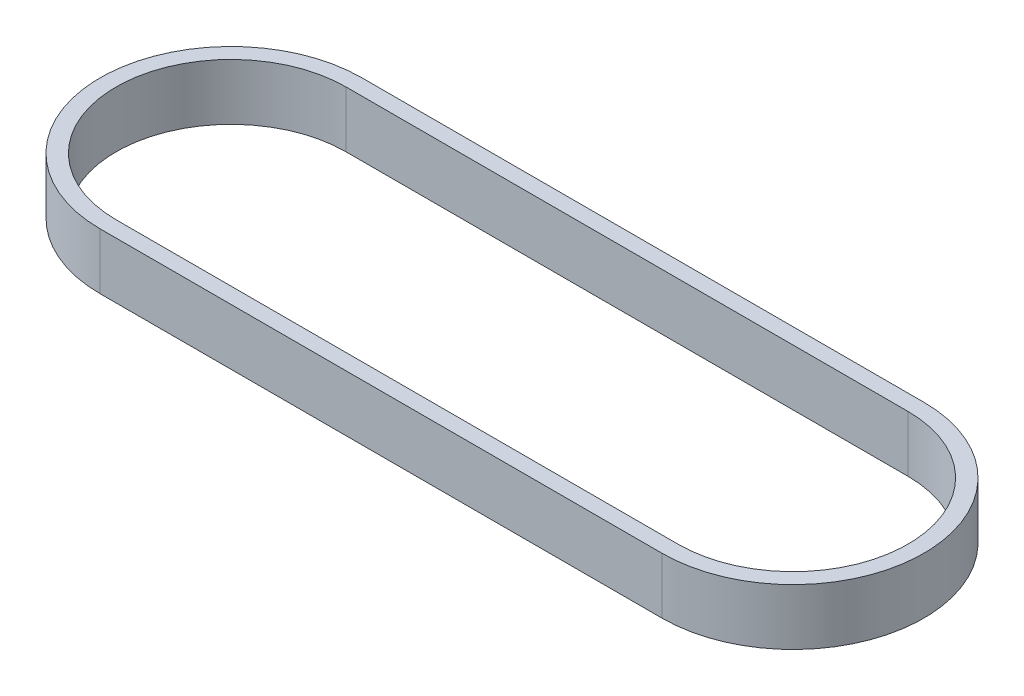
SolidWorks part; units mm, degrees
ref_plane "Front Plane" through (0, 0, 0) normal (0, 0, 1) x (1, 0, 0)
ref_plane "Top Plane" through (0, 0, 0) normal (0, 1, 0) x (1, 0, 0)
ref_plane "Right Plane" through (0, 0, 0) normal (1, 0, 0) x (0, 0, -1)
sketch "Sketch1" plane through (0, 0, 0) normal (0, 1, 0) x (1, 0, 0)
  line L0 (44.9999, 0) -> (-44.9999, 0) construction
  line L1 (44.9999, -20.955) -> (-44.9999, -20.955)
  line L2 (44.9999, 20.955) -> (-44.9999, 20.955)
  line L3 (44.9999, -18.415) -> (-44.9999, -18.415)
  line L4 (44.9999, 18.415) -> (-44.9999, 18.415)
  arc A0 (44.9999, -20.955) -> (44.9999, 20.955) centre (44.9999, 0) ccw
  arc A1 (-44.9999, 20.955) -> (-44.9999, -20.955) centre (-44.9999, 0) ccw
  arc A2 (-44.9999, 18.415) -> (-44.9999, -18.415) centre (-44.9999, 0) ccw
  arc A3 (44.9999, -18.415) -> (44.9999, 18.415) centre (44.9999, 0) ccw
  point P2 (0, 0)
  dimension "D1" = 41.91
  dimension "D2" = 89.9998
  dimension "D3" = 2.54
extrude "Boss-Extrude1" add sketch "Sketch1" along normal blind 9
